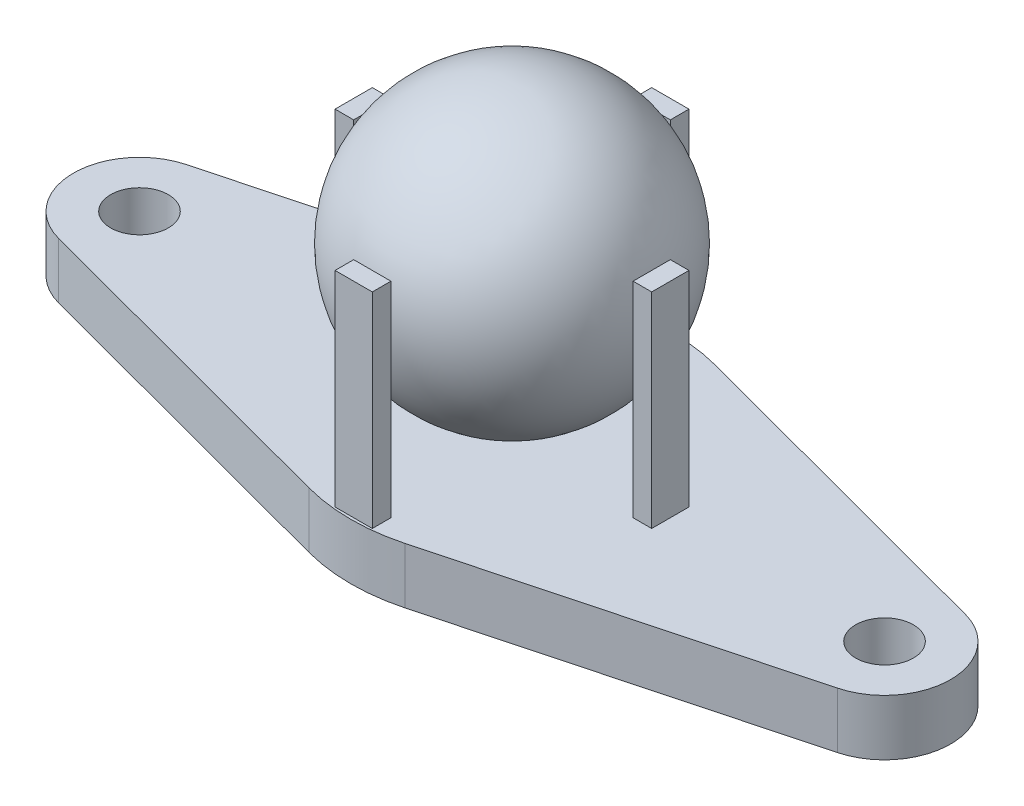
SolidWorks part; units mm, degrees
ref_plane "Front Plane" through (0, 0, 0) normal (0, 0, 1) x (1, 0, 0)
ref_plane "Top Plane" through (0, 0, 0) normal (0, 1, 0) x (1, 0, 0)
ref_plane "Right Plane" through (0, 0, 0) normal (1, 0, 0) x (0, 0, -1)
sketch "Sketch2" plane through (0, 0, 0) normal (0, 1, 0) x (1, 0, 0)
  line L0 (0, -3.8176) -> (0, 9.1167) construction
  line L1 (-20.9136, 3.4304) -> (0, 9)
  line L2 (-30.5978, 0) -> (29.8571, 0) construction
  line L3 (-23.55, 0) -> (-23.55, -4.3433) construction
  line L4 (-20.9136, -3.4304) -> (0, -9)
  line L5 (23.55, 0) -> (23.55, -4.3433) construction
  line L6 (20.9136, -3.4304) -> (0, -9)
  line L7 (20.9136, 3.4304) -> (0, 9)
  circle A0 centre (-20, 0) radius 1.55
  arc A1 (-20.9136, -3.4304) -> (-20.9136, 3.4304) centre (-20, 0) cw
  arc A2 (20.9136, -3.4304) -> (20.9136, 3.4304) centre (20, 0) ccw
  circle A3 centre (20, 0) radius 1.55
  dimension "D1" = 3.1
  dimension "D3" = 2
  dimension "D2" = 40
  dimension "D4" = 18
extrude "Boss-Extrude1" add sketch "Sketch2" along normal blind 3
fillet "Fillet1" radius 10 2 edges at (0, 1.5, -9) (0, 1.5, 9)
sketch "Sketch3" plane through (0, 0, 0) normal (0, 0, 1) x (1, 0, 0)
  line L0 (0, 0) -> (0, 10.1661) construction
  line L1 (-2.5734, 0) -> (2.5734, 0) construction
  line L2 (2.5734, 3) -> (-2.5734, 3) construction
  line L3 (0, 19) -> (0, 4)
  arc A0 (0, 4) -> (0, 19) centre (0, 11.5) cw
  dimension "D1" = 19
  dimension "D2" = 1
revolve "Revolve1" add sketch "Sketch3" angle 360 about L0
sketch "Sketch4" plane through (0, 3, 0) normal (0, 1, 0) x (1, 0, 0)
  line L1 (-1, 8.5) -> (1, 8.5)
  line L2 (-1, 8.5) -> (-1, 7.5)
  line L3 (-1, 7.5) -> (1, 7.5)
  line L4 (1, 8.5) -> (1, 7.5)
  line L16 (-22.7634, 0) -> (20, 0) construction
  line L17 (0, 11.7348) -> (0, -13.8467) construction
  line L22 (8.5, 1) -> (8.5, -1)
  line L23 (8.5, 1) -> (7.5, 1)
  line L24 (7.5, 1) -> (7.5, -1)
  line L25 (8.5, -1) -> (7.5, -1)
  line L26 (1, -8.5) -> (-1, -8.5)
  line L27 (1, -8.5) -> (1, -7.5)
  line L28 (1, -7.5) -> (-1, -7.5)
  line L29 (-1, -8.5) -> (-1, -7.5)
  line L30 (-8.5, -1) -> (-8.5, 1)
  line L31 (-8.5, -1) -> (-7.5, -1)
  line L32 (-7.5, -1) -> (-7.5, 1)
  line L33 (-8.5, 1) -> (-7.5, 1)
  circle A0 centre (0, 0) radius 7.5 construction
  circle A2 centre (0, 0) radius 7.5 construction
  point P7 (0, 8.5)
  dimension "D1" = 1
  dimension "D2" = 2
  dimension "D3" = 4
extrude "Boss-Extrude2" add sketch "Sketch4" along normal blind 11
